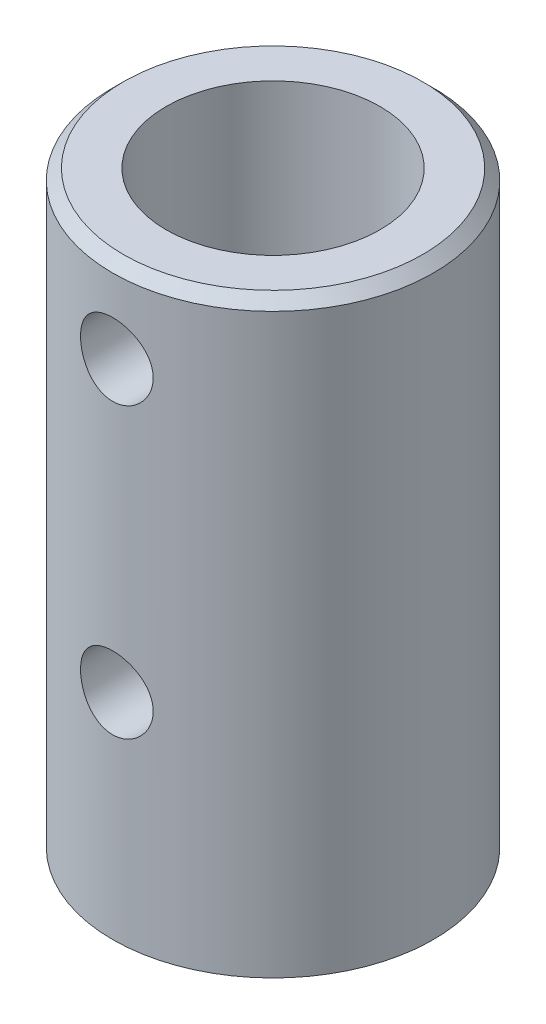
SolidWorks part; units mm, degrees
material "AISI 1020 Steel, Cold Rolled"
ref_plane "Front Plane" through (0, 0, 0) normal (0, 0, 1) x (1, 0, 0)
ref_plane "Top Plane" through (0, 0, 0) normal (0, 1, 0) x (1, 0, 0)
ref_plane "Right Plane" through (0, 0, 0) normal (1, 0, 0) x (0, 0, -1)
sketch "Sketch1" plane through (0, 0, 0) normal (0, 1, 0) x (1, 0, 0)
  circle A0 centre (0, 0) radius 10
  circle A1 centre (0, 0) radius 15
  dimension "D1" = 20
  dimension "D2" = 30
extrude "Boss-Extrude1" add sketch "Sketch1" along normal blind 55
ref_plane "Plane1" through (0, 0, 15) normal (0, 0, 1) x (1, 0, 0)
hole_wizard "M8 Tapped Hole1" positions "Sketch2" profile "Sketch3" tap size "M8" standard "ISO"
sketch "Sketch2" plane through (0, 0, 15) normal (0, 0, 1) x (1, 0, 0)
  line L0 (10, 55) -> (-10, 55) construction
  point P0 (0, 47)
  point P2 (0, 20)
  dimension "D1" = 20
  dimension "D2" = 8
sketch "Sketch3" plane through (0, 47, 15) normal (1, 0, 0) x (0, -1, 0)
  line L0 (0, 0) -> (0, 5)
  line L1 (0, 5) -> (3.4, 5)
  line L2 (3.4, 5) -> (3.4, 0)
  line L5 (3.4, 0) -> (0, 0)
  line L11 (0, -6.35) -> (0, 107.95) construction
  dimension "Thru Tap Drill Dia." = 6.8
  dimension "Thru Tap Drill Depth" = 5
cosmetic thread "Hole Thread1"
cosmetic thread "Hole Thread2"
chamfer "Chamfer1" distance 1 angle 45 1 edges at (0, 55, 15)
